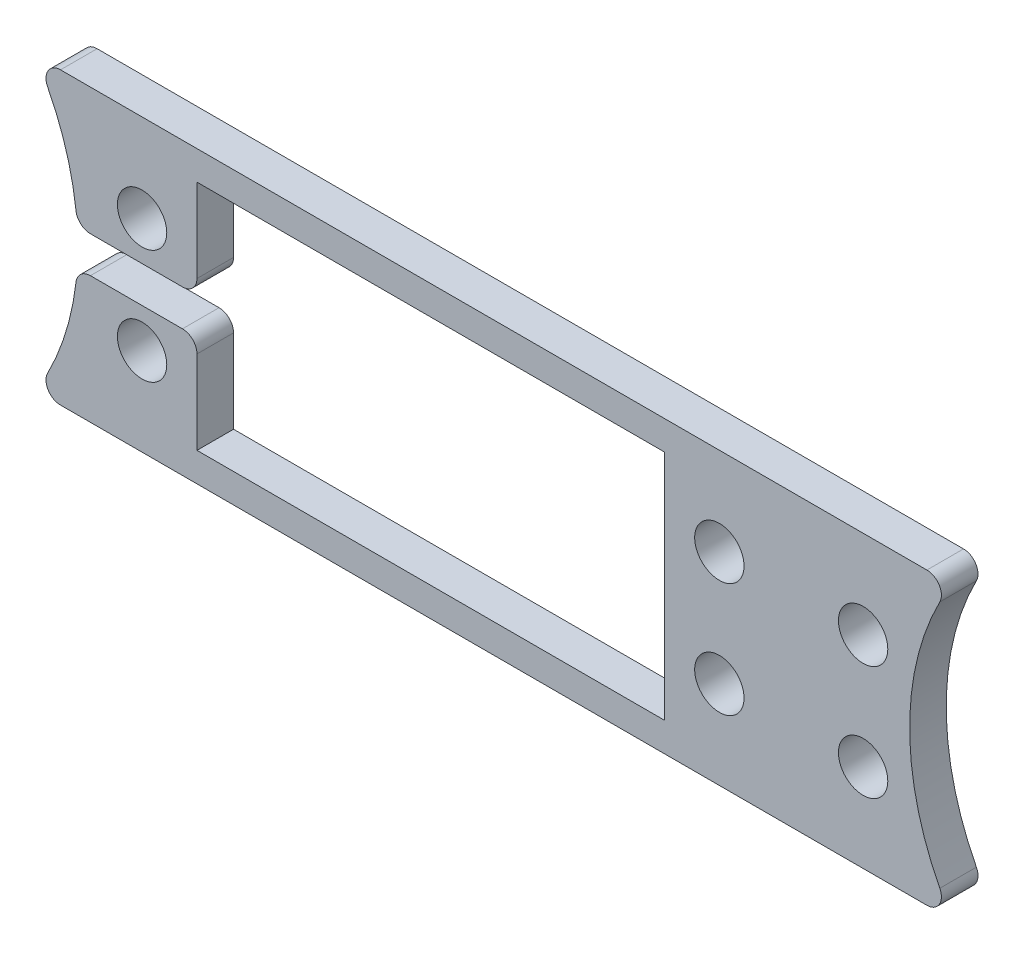
SolidWorks part; units mm, degrees
ref_plane "Front Plane" through (0, 0, 0) normal (0, 0, 1) x (1, 0, 0)
ref_plane "Top Plane" through (0, 0, 0) normal (0, 1, 0) x (1, 0, 0)
ref_plane "Right Plane" through (0, 0, 0) normal (1, 0, 0) x (0, 0, -1)
sketch "Sketch1" plane through (0, 0, 0) normal (0, 0, 1) x (1, 0, 0)
  line L0 (14.1324, 22.86) -> (55.0264, 22.86)
  line L1 (0, 25.4) -> (80.1799, 25.4)
  line L2 (0, 25.4) -> (0, 0) construction
  line L3 (0, 0) -> (80.1799, 0)
  line L4 (80.1799, 25.4) -> (80.1799, 0) construction
  line L5 (14.1324, 22.86) -> (14.1324, 2.54)
  line L6 (14.1324, 2.54) -> (55.0264, 2.54)
  line L7 (55.0264, 22.86) -> (55.0264, 2.54)
  line L8 (-19.9176, 12.7) -> (100.0974, 12.7) construction
  line L9 (34.5794, 22.86) -> (34.5794, 2.54) construction
  arc A0 (0, 25.4) -> (0, 0) centre (-19.9176, 12.7) cw
  arc A1 (80.1799, 0) -> (80.1799, 25.4) centre (100.0974, 12.7) cw
  point P11 (34.5794, 12.7)
  point P12 (24.5324, 12.7)
  dimension "D3" = 10.4
  dimension "D4" = 20.32
  dimension "D7" = 23.622
  dimension "D1" = 120.015
  dimension "D2" = 25.4
  dimension "D5" = 40.894
  dimension "D6" = 44.45
extrude "Boss-Extrude1" add sketch "Sketch1" along normal blind 3.2004
sketch "Sketch2" plane through (0, 0, 3.2004) normal (0, 0, 1) x (1, 0, 0)
  line L5 (34.5794, 22.86) -> (34.5794, 2.54) construction
  line L13 (9.3294, 7.7) -> (9.3294, 17.7) construction
  line L14 (59.8294, 7.7) -> (59.8294, 17.7) construction
  line L15 (9.3294, 12.7) -> (59.8294, 12.7) construction
  line L18 (59.8294, 12.7) -> (72.4047, 12.7) construction
  line L19 (72.4047, 7.7) -> (72.4047, 17.7) construction
  circle A0 centre (9.3294, 17.7) radius 2.159
  circle A1 centre (59.8294, 7.7) radius 2.159
  circle A2 centre (59.8294, 17.7) radius 2.159
  circle A3 centre (9.3294, 7.7) radius 2.159
  circle A4 centre (72.4047, 17.7) radius 2.159
  circle A5 centre (72.4047, 7.7) radius 2.159
  dimension "D2" = 4.318
  dimension "D3" = 12.5752
  dimension "D1" = 50.5
  dimension "D7" = 10
extrude "Cut-Extrude1" cut sketch "Sketch2" against normal up to surface (3.2004 mm away) up to face at (40.0899, 12.7, 0)
sketch "Sketch3" plane through (0, 0, 3.2004) normal (0, 0, 1) x (1, 0, 0)
  line L0 (14.1324, 22.86) -> (14.1324, 2.54) construction
  line L1 (3.651, 14.2875) -> (14.1324, 14.2875)
  line L2 (3.651, 14.2875) -> (3.651, 11.1125)
  line L3 (3.651, 11.1125) -> (14.1324, 11.1125)
  line L4 (14.1324, 14.2875) -> (14.1324, 11.1125)
  arc A0 (0, 0) -> (0, 25.4) centre (-19.9176, 12.7) ccw construction
  point P1 (14.1324, 12.7)
  dimension "D1" = 3.175
extrude "Cut-Extrude2" cut sketch "Sketch3" against normal up to surface (3.2004 mm away) up to face at (57.6704, 17.7, 0)
fillet "Fillet1" radius 1.27 8 edges at (0, 0, 1.6002) (0, 25.4, 1.6002) (80.1799, 0, 1.6002) (80.1799, 25.4, 1.6002) (3.651, 11.1125, 1.6002) (3.651, 14.2875, 1.6002) (14.1324, 11.1125, 1.6002) (14.1324, 14.2875, 1.6002)
